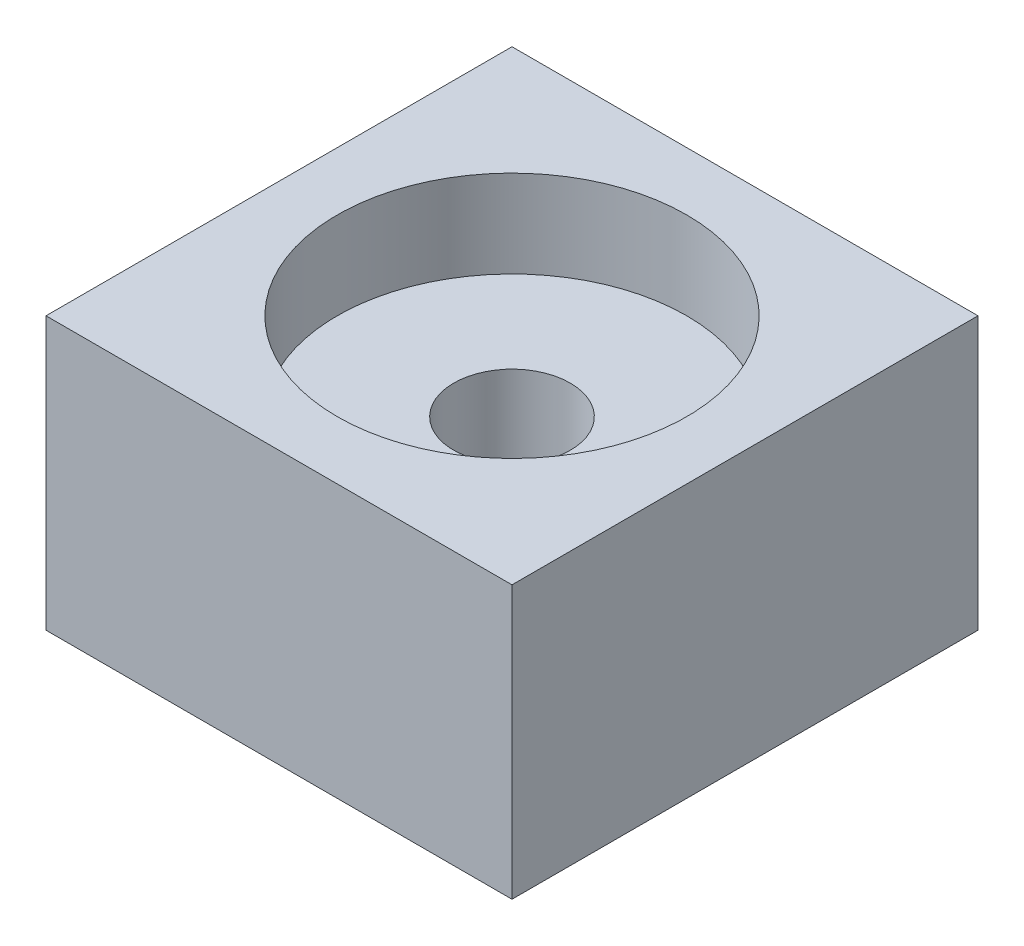
SolidWorks part; units mm, degrees
ref_plane "Front Plane" through (0, 0, 0) normal (0, 0, 1) x (1, 0, 0)
ref_plane "Top Plane" through (0, 0, 0) normal (0, 1, 0) x (1, 0, 0)
ref_plane "Right Plane" through (0, 0, 0) normal (1, 0, 0) x (0, 0, -1)
sketch "Sketch1" plane through (0, 0, 0) normal (0, 1, 0) x (1, 0, 0)
  line L1 (0, 0) -> (16, 0)
  line L2 (0, 0) -> (0, 16)
  line L3 (0, 16) -> (16, 16)
  line L4 (16, 0) -> (16, 16)
  circle A0 centre (8, 8) radius 6
  point P7 (0, 0)
  point P8 (8, 0)
  point P9 (0, 0)
  point P10 (0, 8)
  point P11 (14.8744, 12.7637)
  point P14 (31.2452, 30.4441)
  dimension "D1" = 12
  dimension "D2" = 8
  dimension "D3" = 8
extrude "Boss-Extrude1" add sketch "Sketch1" along normal blind 3
sketch "Sketch2" plane through (0, 0, 0) normal (0, -1, 0) x (1, 0, 0)
  line L1 (0, 0) -> (16, 0)
  line L2 (0, 0) -> (0, -16)
  line L3 (0, -16) -> (16, -16)
  line L4 (16, 0) -> (16, -16)
extrude "Boss-Extrude2" add sketch "Sketch2" along normal blind 6.35
sketch "Sketch3" plane through (0, -6.35, 0) normal (0, -1, 0) x (1, 0, 0)
  line L0 (16, 0) -> (0, 0) construction
  line L1 (0, 0) -> (0, -16) construction
  circle A0 centre (8, -8) radius 2
  point P2 (0, 0)
  point P5 (8, 0)
  point P6 (0, 0)
  point P9 (0, -8)
  dimension "D1" = 4
extrude "Cut-Extrude1" cut sketch "Sketch3" against normal blind 6.35
